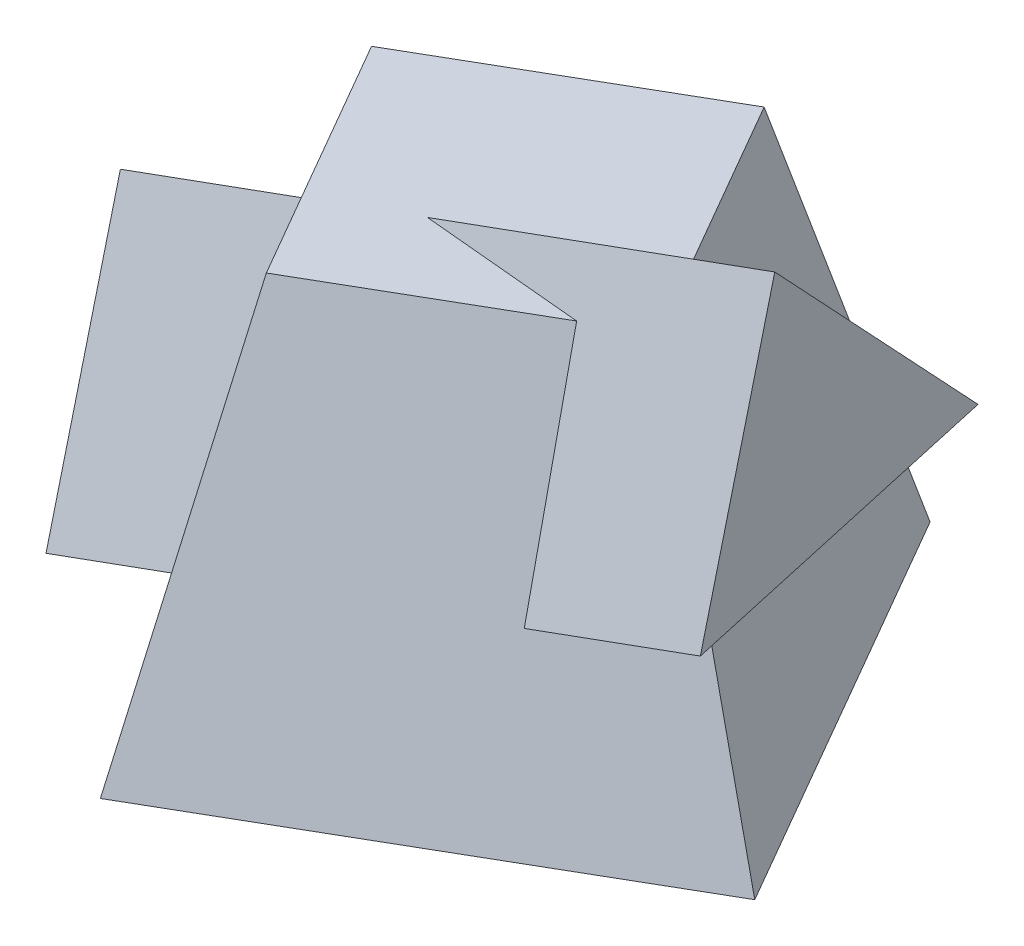
SolidWorks part; units mm, degrees
ref_plane "Front" through (0, 0, 0) normal (0, 0, 1) x (1, 0, 0)
ref_plane "Top" through (0, 0, 0) normal (0, 1, 0) x (1, 0, 0)
ref_plane "Right" through (0, 0, 0) normal (1, 0, 0) x (0, 0, -1)
sketch "Sketch1" plane through (0, 0, 0) normal (0, 1, 0) x (1, 0, 0)
  line L0 (0, 0) -> (-86.6025, -50)
  line L1 (-86.6025, -50) -> (-36.6025, -136.6025)
  line L2 (-36.6025, -136.6025) -> (50, -86.6025)
  line L3 (50, -86.6025) -> (0, 0)
  line L4 (0, 0) -> (-42.4152, 0) construction
  dimension "D1" = 100
  dimension "D2" = 30
ref_plane "Plane1" through (0, 85, 0) normal (0, 1, 0) x (-1, 0, 0)
sketch "Sketch2" plane through (0, 85, 0) normal (0, 1, 0) x (-1, 0, 0)
  line L6 (59.282, 57.3205) -> (7.3205, 27.3205)
  line L7 (7.3205, 27.3205) -> (-22.6795, 79.282)
  line L8 (-22.6795, 79.282) -> (29.282, 109.282)
  line L9 (29.282, 109.282) -> (59.282, 57.3205)
loft "Pyramid" add profiles "Sketch2", "Sketch1"
sketch "Sketch3" plane through (0, 0, 0) normal (0, 1, 0) x (1, 0, 0)
  line L0 (-86.6025, -2.38) -> (-86.6025, -94.9268) construction
ref_plane "Plane2" through (-76.472, -27.8335, 0) normal (0.9397, 0.342, 0) x (0, 0, -1)
sketch "Sketch4" plane through (-76.472, -27.8335, 0) normal (0.9397, 0.342, 0) x (0, 0, -1)
  line L0 (-97.9555, 29.6198) -> (-40, 45.149)
  line L1 (-2.38, 29.6198) -> (-94.9268, 29.6198) construction
  line L2 (-40, 45.149) -> (-82.4264, 87.5754)
  line L3 (-82.4264, 87.5754) -> (-97.9555, 29.6198)
  dimension "D1" = 40
  dimension "D2" = 60
  dimension "D3" = 15
extrude "Triangular Prism" add sketch "Sketch4" along normal blind 170
sketch "Sketch5" plane through (0, 0, 0) normal (0, 0, 1) x (1, 0, 0)
  line L1 (-86.6025, 0) -> (-107.4338, 0)
  line L2 (-86.6025, 0) -> (-86.6025, 63.4852)
  line L3 (-86.6025, 63.4852) -> (-107.4338, 63.4852)
  line L4 (-107.4338, 0) -> (-107.4338, 63.4852)
  line L5 (50, 0) -> (75.6507, 0)
  line L6 (50, 0) -> (50, 114.2462)
  line L7 (50, 114.2462) -> (75.6507, 114.2462)
  line L8 (75.6507, 0) -> (75.6507, 114.2462)
extrude "Cut-Extrude1" cut sketch "Sketch5" along normal blind 100
